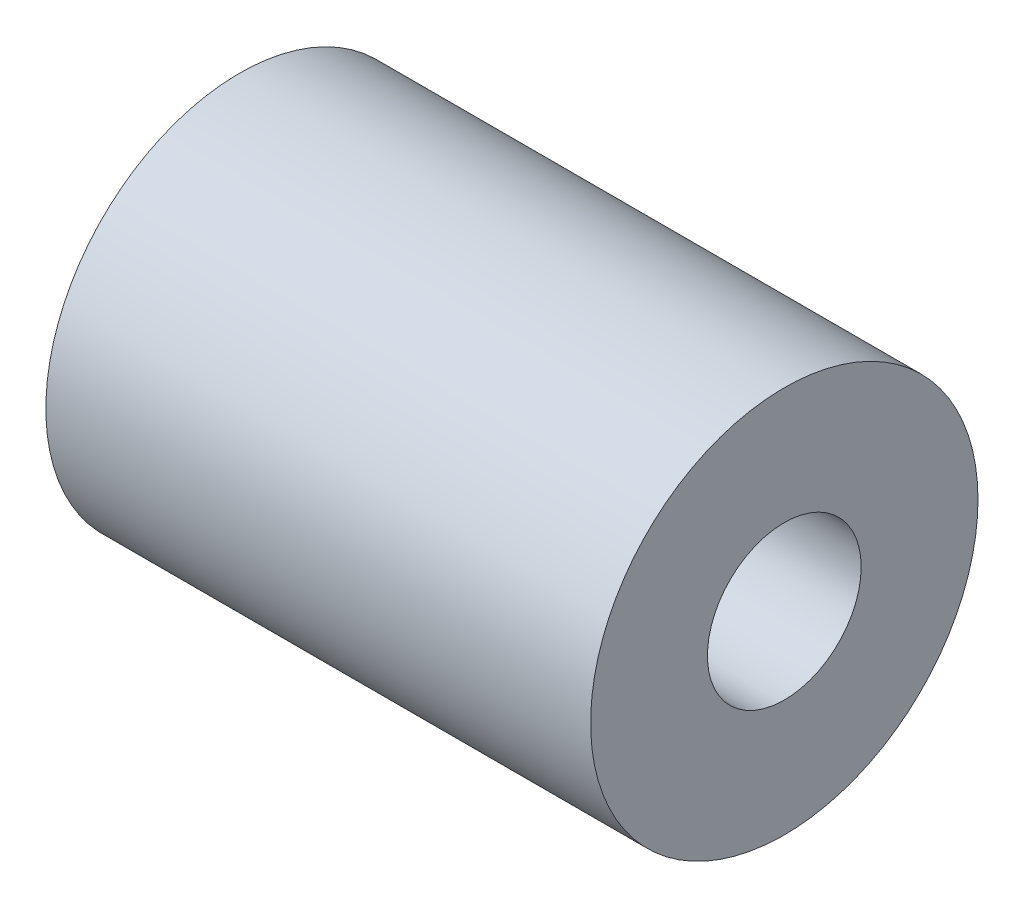
SolidWorks part; units mm, degrees
ref_plane "Front Plane" through (0, 0, 0) normal (0, 0, 1) x (1, 0, 0)
ref_plane "Top Plane" through (0, 0, 0) normal (0, 1, 0) x (1, 0, 0)
ref_plane "Right Plane" through (0, 0, 0) normal (1, 0, 0) x (0, 0, -1)
sketch "Sketch1" plane through (0, 0, 0) normal (1, 0, 0) x (0, 0, -1)
  circle A0 centre (0, 0) radius 8
  circle A1 centre (0, 0) radius 2.5
  dimension "D1" = 16
  dimension "D2" = 5
extrude "Boss-Extrude1" add sketch "Sketch1" along normal mid plane 22.5
sketch "Sketch2" plane through (11.25, 0, 0) normal (1, 0, 0) x (0, 0, -1)
  circle A0 centre (0, 0) radius 3.175
  dimension "D1" = 6.35
extrude "Cut-Extrude1" cut sketch "Sketch2" against normal blind 11.25
sketch "Sketch3" plane through (0, 0, 0) normal (1, 0, 0) x (0, 0, -1)
  circle A0 centre (0, 0) radius 8 construction
  circle A1 centre (0, 0) radius 8
extrude "Boss-Extrude2" add sketch "Sketch3" along normal offset from surface 6.35 and the other way offset from surface (4.9 mm away) 6.35 up to face at (11.25, 0, -3.175) other way up to face at (-11.25, 0, -8)
